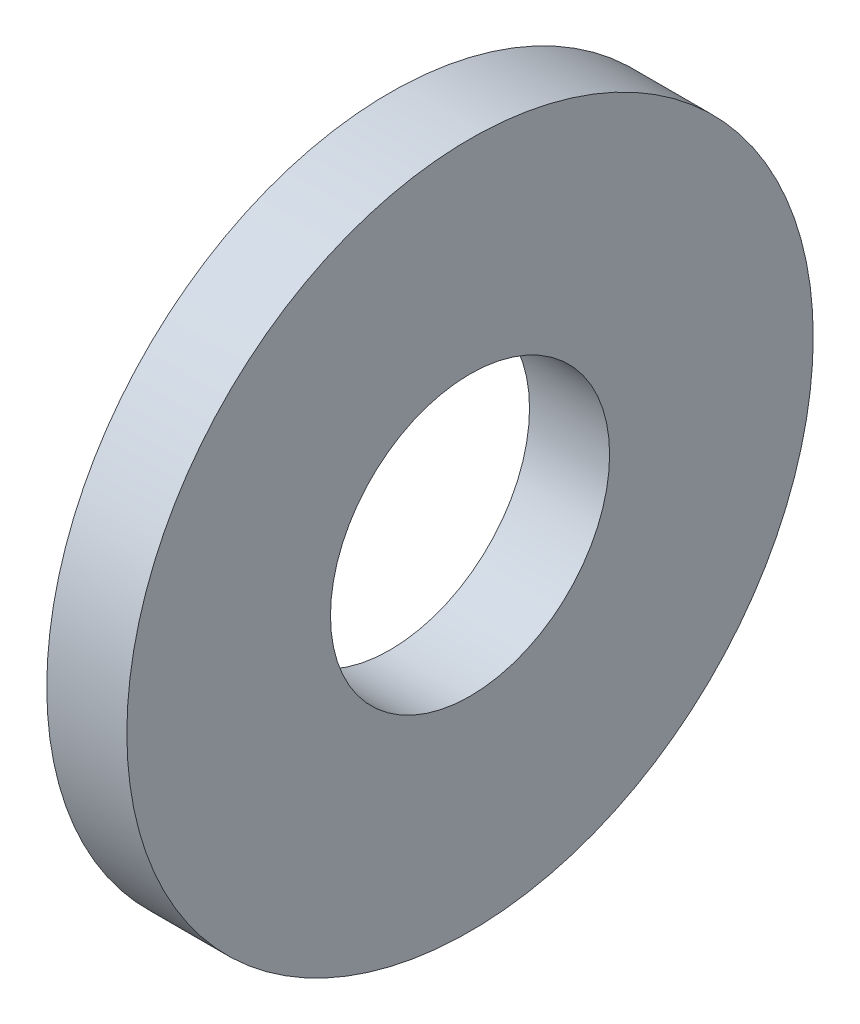
SolidWorks part; units mm, degrees
ref_plane "Plane1" through (0, 0, 0) normal (0, 0, 1) x (1, 0, 0)
ref_plane "Plane2" through (0, 0, 0) normal (0, 1, 0) x (1, 0, 0)
ref_plane "Plane3" through (0, 0, 0) normal (1, 0, 0) x (0, 0, -1)
other "Configuration Table"
sketch "Sketch1" plane through (0, 0, 0) normal (0, 0, 1) x (1, 0, 0)
  line L0 (-34.925, 0) -> (9.525, 0) construction
  line L1 (0, 2.44) -> (0, 6)
  line L2 (0, 6) -> (-1.4, 6)
  line L3 (-1.4, 6) -> (-1.4, 2.44)
  line L4 (-1.4, 2.44) -> (0, 2.44)
  dimension "Thickness" = 1.4
  dimension "Inside_dia" = 4.88
  dimension "Outside_dia" = 12
revolve "Base-Revolve" add sketch "Sketch1" angle 360 about L0
